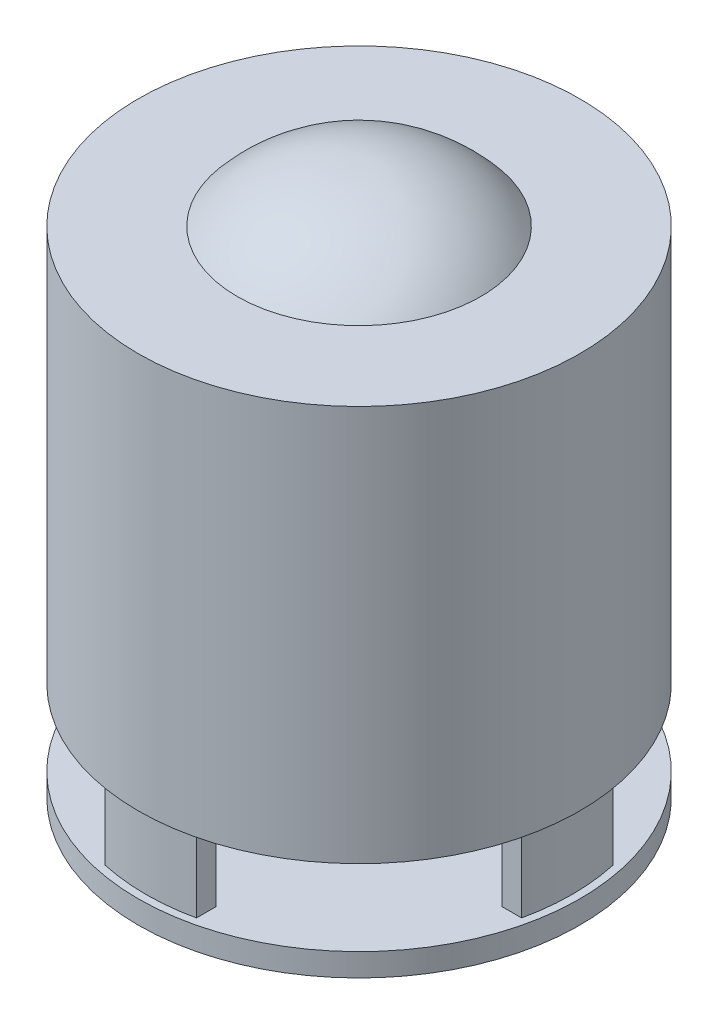
SolidWorks part; units mm, degrees
ref_plane "Front" through (0, 0, 0) normal (0, 0, 1) x (1, 0, 0)
ref_plane "Top" through (0, 0, 0) normal (0, 1, 0) x (1, 0, 0)
ref_plane "Right" through (0, 0, 0) normal (1, 0, 0) x (0, 0, -1)
sketch "Sketch1" plane through (0, 0, 0) normal (0, 1, 0) x (1, 0, 0)
  circle A0 centre (0, 0) radius 29
  dimension "D1" = 58
extrude "Boss-Extrude1" add sketch "Sketch1" along normal blind 3
sketch "Sketch2" plane through (0, 3, 0) normal (0, 1, 0) x (1, 0, 0)
  line L0 (0, 29) -> (0, -29) construction
  line L1 (-29, 0) -> (29, 0) construction
  line L2 (-29, -6) -> (29, -6)
  line L3 (-29, 6) -> (29, 6)
  line L4 (-6, 29) -> (-6, -29)
  line L5 (6, 29) -> (6, -29)
  circle A0 centre (0, 0) radius 25.5
  circle A1 centre (0, 0) radius 29
  circle A2 centre (0, 0) radius 29
  circle A3 centre (0, 0) radius 28
  dimension "D3" = 6
  dimension "D1" = 0
  dimension "D2" = 3.5
  dimension "D4" = 6
  dimension "D5" = 6
  dimension "D6" = 6
  dimension "D7" = 1
extrude "Boss-Extrude2" add sketch "Sketch2" along normal blind 10 contours L3 A3 L2 A0 | L5 A3 L4 A0 | L2 A3 L3 A0 | L4 A3 L5 A0
sketch "Sketch3" plane through (0, 13, 0) normal (0, 1, 0) x (1, 0, 0)
  circle A1 centre (0, 0) radius 29
  dimension "D1" = 58
extrude "Boss-Extrude3" add sketch "Sketch3" along normal blind 52
sketch "Sketch4" plane through (0, 0, 0) normal (0, 0, 1) x (1, 0, 0)
  line L0 (0, 65) -> (0, 72)
  line L1 (29, 65) -> (-29, 65) construction
  line L2 (0, 65) -> (16, 65)
  arc A0 (0, 72) -> (16, 65) centre (0.788, 52.0155) cw
  dimension "D3" = 20
  dimension "D1" = 7
  dimension "D2" = 16
revolve "Revolve1" add sketch "Sketch4" angle 360 about L0
sketch "Sketch5" plane through (0, 0, 0) normal (0, -1, 0) x (1, 0, 0)
  line L0 (0, 0) -> (0, 12) construction
  line L1 (0, 0) -> (10.3923, -6) construction
  line L2 (0, 0) -> (-10.3923, -6) construction
  circle A0 centre (0, 12) radius 2.05
  circle A1 centre (10.3923, -6) radius 2.05
  circle A2 centre (-10.3923, -6) radius 2.05
  point P13 (0, 0)
  dimension "D2" = 4.1
  dimension "D1" = 12
  dimension "D3" = 3
extrude "Cut-Extrude1" cut sketch "Sketch5" against normal blind 5
